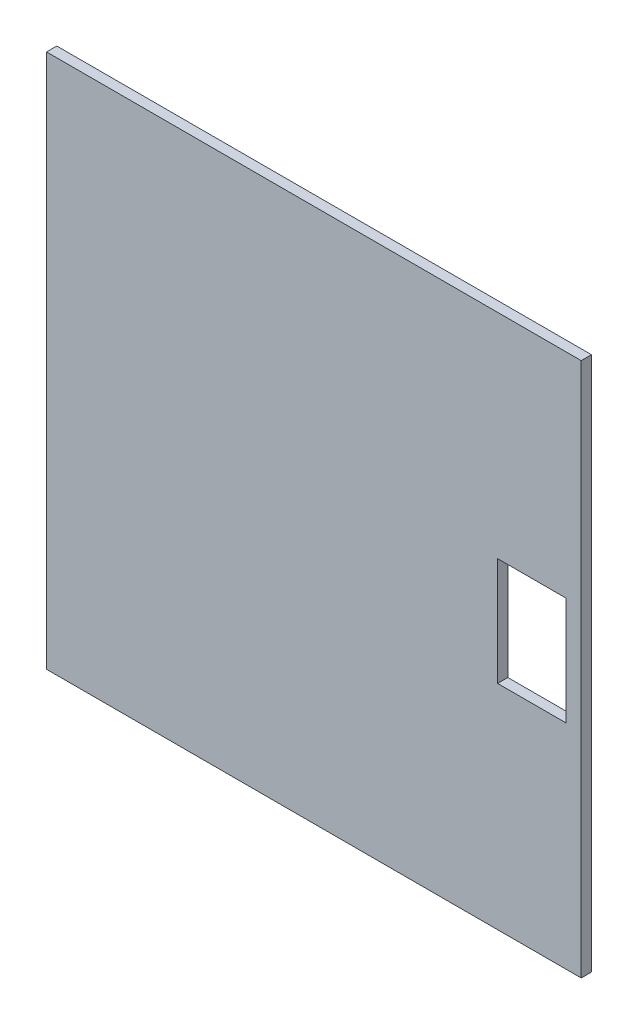
SolidWorks part; units mm, degrees
ref_plane "Płaszczyzna przednia" through (0, 0, 0) normal (0, 0, 1) x (1, 0, 0)
ref_plane "Płaszczyzna górna" through (0, 0, 0) normal (0, 1, 0) x (1, 0, 0)
ref_plane "Płaszczyzna prawa" through (0, 0, 0) normal (1, 0, 0) x (0, 0, -1)
sketch "Szkic1" plane through (0, 0, 0) normal (0, 0, 1) x (1, 0, 0)
  line L1 (0, 0) -> (470, 0)
  line L2 (0, 0) -> (0, 470)
  line L3 (0, 470) -> (470, 470)
  line L4 (470, 0) -> (470, 470)
  dimension "D1" = 470
  dimension "D2" = 470
extrude "Dodanie-wyciągnięcie2" add sketch "Szkic1" against normal blind 9
sketch "Szkic4" plane through (0, 0, 0) normal (0, 0, 1) x (1, 0, 0)
  line L0 (65, 395) -> (385, 395)
  line L1 (65, 395) -> (65, 75)
  line L2 (65, 75) -> (385, 75)
  line L3 (385, 395) -> (385, 75)
  line L4 (406.5, 272.5) -> (446.5, 272.5)
  line L5 (406.5, 272.5) -> (406.5, 197.5)
  line L6 (406.5, 197.5) -> (446.5, 197.5)
  line L7 (446.5, 272.5) -> (446.5, 197.5)
  line L8 (470, 470) -> (0, 470) construction
  line L9 (470, 0) -> (470, 470) construction
  line L10 (345, 75) -> (345, 395)
  line L11 (305, 75) -> (305, 395)
  line L12 (265, 75) -> (265, 395)
  line L13 (456.5, 282.5) -> (396.5, 282.5)
  line L14 (456.5, 282.5) -> (456.5, 187.5)
  line L15 (456.5, 187.5) -> (396.5, 187.5)
  line L16 (396.5, 282.5) -> (396.5, 187.5)
  line L17 (225, 75) -> (225, 395)
  line L18 (105, 75) -> (105, 395)
  line L19 (145, 75) -> (145, 395)
  line L20 (185, 75) -> (185, 395)
  line L21 (65, 115) -> (385, 115)
  line L22 (65, 155) -> (385, 155)
  line L23 (65, 195) -> (385, 195)
  line L24 (65, 235) -> (385, 235)
  line L25 (65, 355) -> (385, 355)
  line L26 (65, 315) -> (385, 315)
  line L27 (65, 275) -> (385, 275)
  line L28 (0, 470) -> (0, 0) construction
  dimension "D9" = 40
  dimension "D12" = 40
  dimension "D7" = 187.5
  dimension "D1" = 320
  dimension "D2" = 320
  dimension "D3" = 40
  dimension "D4" = 75
  dimension "D5" = 75
  dimension "D6" = 65
  dimension "D8" = 23.5
  dimension "D10" = 40
  dimension "D11" = 40
  dimension "D13" = 40
  dimension "D14" = 40
  dimension "D15" = 95
  dimension "D16" = 60
  dimension "D17" = 10
  dimension "D18" = 10
  dimension "D19" = 40
  dimension "D20" = 40
  dimension "D21" = 85
sketch "Szkic5" plane through (0, 0, 0) normal (0, 0, 1) x (1, 0, 0)
  line L1 (396.5, 282.5) -> (456.5, 282.5)
  line L2 (396.5, 282.5) -> (396.5, 187.5)
  line L3 (396.5, 187.5) -> (456.5, 187.5)
  line L4 (456.5, 282.5) -> (456.5, 187.5)
extrude "Wytnij-wyciągnięcie1" cut sketch "Szkic5" against normal blind 10
